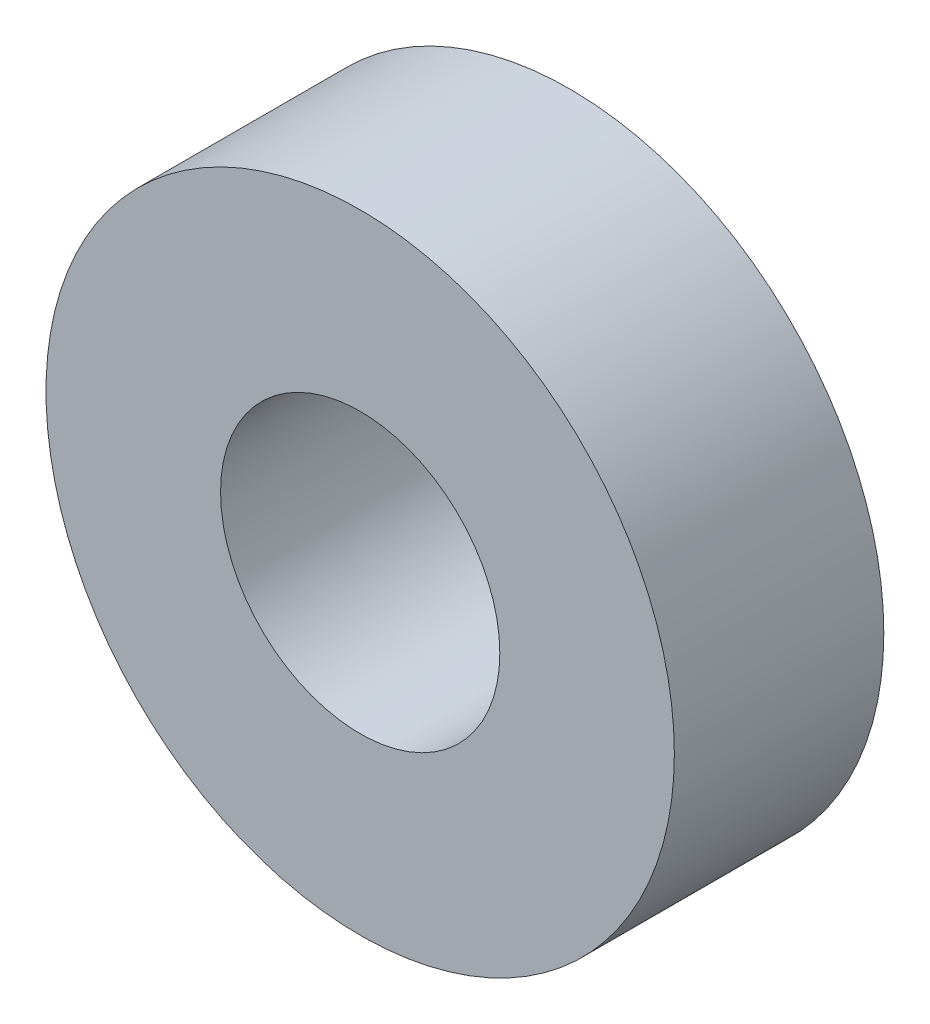
SolidWorks part; units mm, degrees
ref_plane "Front Plane" through (0, 0, 0) normal (0, 0, 1) x (1, 0, 0)
ref_plane "Top Plane" through (0, 0, 0) normal (0, 1, 0) x (1, 0, 0)
ref_plane "Right Plane" through (0, 0, 0) normal (1, 0, 0) x (0, 0, -1)
sketch "Sketch1" plane through (0, 0, 0) normal (0, 0, 1) x (1, 0, 0)
  circle A0 centre (0, 0) radius 1
  circle A1 centre (0, 0) radius 2.25
  dimension "D1" = 2
  dimension "D2" = 4.5
extrude "Boss-Extrude1" add sketch "Sketch1" along normal blind 1.5 contours A1 A0
